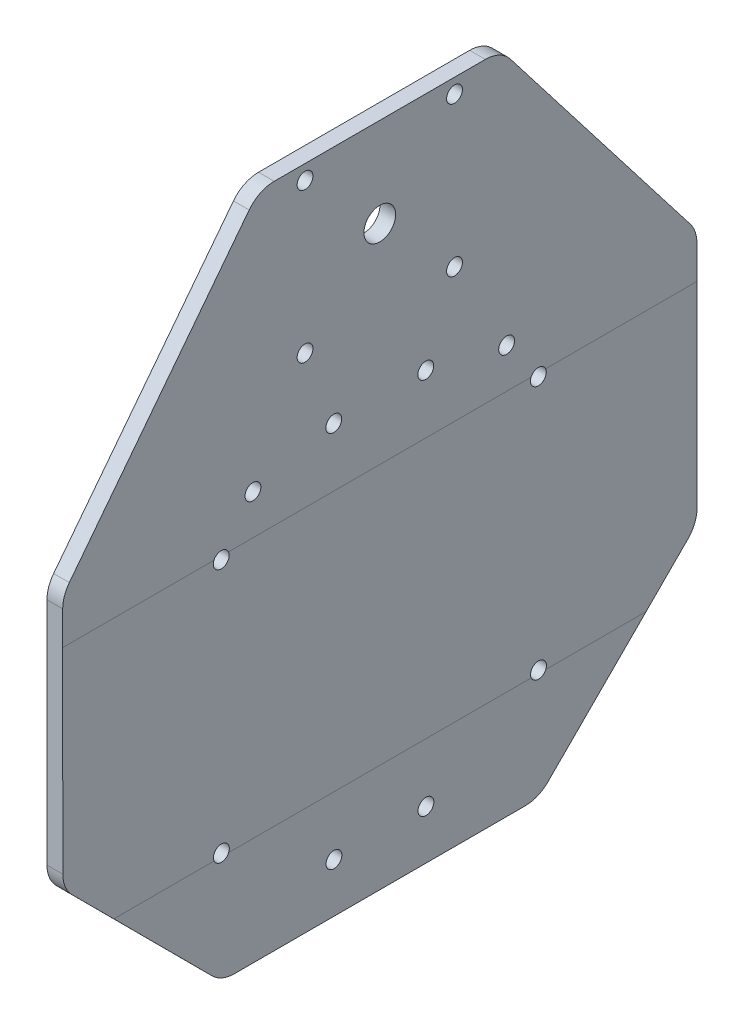
SolidWorks part; units mm, degrees
ref_plane "Alzado" through (0, 0, 0) normal (0, 0, 1) x (1, 0, 0)
ref_plane "Planta" through (0, 0, 0) normal (0, 1, 0) x (1, 0, 0)
ref_plane "Vista lateral" through (0, 0, 0) normal (1, 0, 0) x (0, 0, -1)
sketch "Croquis1" plane through (0, 0, 0) normal (0, 0, 1) x (1, 0, 0)
  line L0 (108.156, -24.4012) -> (108.156, 35.6988) construction
  line L5 (108.156, -24.4012) -> (-28.444, -24.4012) construction
  line L6 (108.156, 35.6988) -> (-28.444, 35.6988) construction
  line L7 (-28.444, -24.4012) -> (-28.444, 35.6988) construction
  line L8 (39.856, 35.6988) -> (39.856, -24.4012) construction
  line L9 (78.056, 5.6488) -> (108.156, 5.6488) construction
  line L10 (81.056, -24.4012) -> (89.106, -24.4012) construction
  line L11 (78.056, -21.4012) -> (78.056, -12.9012) construction
  line L12 (81.056, 35.6988) -> (89.106, 35.6988) construction
  line L13 (108.156, -21.4012) -> (108.156, -12.9012) construction
  line L14 (78.056, -24.4012) -> (108.156, 35.6988) construction
  line L15 (78.056, 35.6988) -> (108.156, -24.4012) construction
  line L16 (89.106, 35.6988) -> (89.106, 33.3988) construction
  line L17 (88.106, 13.6988) -> (98.106, 13.6988) construction
  line L18 (86.606, 15.1988) -> (86.606, 25.1988) construction
  line L19 (88.106, 26.6988) -> (98.106, 26.6988) construction
  line L20 (99.606, 15.1988) -> (99.606, 25.1988) construction
  line L21 (86.606, 13.6988) -> (99.606, 26.6988) construction
  line L22 (86.606, 26.6988) -> (99.606, 13.6988) construction
  line L23 (108.156, 24.1988) -> (108.156, 32.6988) construction
  line L24 (89.756, 16.8488) -> (96.456, 16.8488) construction
  line L25 (89.756, 16.8488) -> (89.756, 23.5488) construction
  line L26 (89.756, 23.5488) -> (96.456, 23.5488) construction
  line L27 (96.456, 16.8488) -> (96.456, 23.5488) construction
  line L28 (89.756, 16.8488) -> (96.456, 23.5488) construction
  line L29 (89.756, 23.5488) -> (96.456, 16.8488) construction
  line L30 (81.406, -22.1012) -> (89.106, -22.1012) construction
  line L31 (80.356, -20.1512) -> (80.356, -12.9012) construction
  line L32 (81.406, 33.3988) -> (89.106, 33.3988) construction
  line L33 (105.856, -20.1512) -> (105.856, -12.9012) construction
  line L34 (80.356, -22.1012) -> (105.856, 33.3988) construction
  line L35 (80.356, 33.3988) -> (105.856, -22.1012) construction
  line L36 (97.106, 35.6988) -> (97.106, 33.3988) construction
  line L37 (105.856, 24.1988) -> (105.856, 31.4488) construction
  line L38 (78.056, 24.1988) -> (80.356, 24.1988) construction
  line L39 (78.056, 16.1988) -> (80.356, 16.1988) construction
  line L40 (108.156, 16.1988) -> (105.856, 16.1988) construction
  line L41 (108.156, 24.1988) -> (105.856, 24.1988) construction
  line L42 (88.106, 26.6988) -> (81.406, 33.3988) construction
  line L43 (86.606, 26.6988) -> (80.356, 33.3988) construction
  line L44 (86.606, 25.1988) -> (80.356, 31.4488) construction
  line L45 (99.606, 25.1988) -> (105.856, 31.4488) construction
  line L46 (98.106, 26.6988) -> (104.806, 33.3988) construction
  line L47 (99.606, -13.9012) -> (105.856, -20.1512) construction
  line L48 (98.106, -15.4012) -> (104.806, -22.1012) construction
  line L49 (78.056, -24.4012) -> (89.106, -24.4012) construction
  line L50 (78.056, 35.6988) -> (89.106, 35.6988) construction
  line L51 (86.606, -13.9012) -> (80.356, -20.1512) construction
  line L52 (88.106, -15.4012) -> (81.406, -22.1012) construction
  line L53 (97.106, -24.4012) -> (97.106, -22.1012) construction
  line L54 (89.106, -24.4012) -> (89.106, -22.1012) construction
  line L55 (78.056, -4.9012) -> (80.356, -4.9012) construction
  line L56 (78.056, -12.9012) -> (80.356, -12.9012) construction
  line L57 (108.156, -12.9012) -> (105.856, -12.9012) construction
  line L58 (108.156, -4.9012) -> (105.856, -4.9012) construction
  line L59 (89.756, -5.5512) -> (89.756, -12.2512) construction
  line L60 (89.756, -12.2512) -> (96.456, -12.2512) construction
  line L61 (96.456, -5.5512) -> (96.456, -12.2512) construction
  line L62 (89.756, -5.5512) -> (96.456, -5.5512) construction
  line L63 (88.106, -2.4012) -> (98.106, -2.4012) construction
  line L64 (99.606, -3.9012) -> (99.606, -13.9012) construction
  line L65 (86.606, -3.9012) -> (86.606, -13.9012) construction
  line L66 (88.106, -15.4012) -> (98.106, -15.4012) construction
  line L67 (97.106, -24.4012) -> (105.156, -24.4012) construction
  line L68 (99.606, -3.9012) -> (105.856, 2.3488) construction
  line L69 (98.106, -2.4012) -> (104.806, 4.2988) construction
  line L70 (88.106, -2.4012) -> (81.406, 4.2988) construction
  line L71 (86.606, -3.9012) -> (80.356, 2.3488) construction
  line L72 (81.406, 4.2988) -> (80.356, 5.3488) construction
  line L73 (104.806, 4.2988) -> (105.856, 5.3488) construction
  line L74 (80.356, 5.3488) -> (80.356, 5.9488) construction
  line L75 (105.856, 5.3488) -> (105.856, 5.9488) construction
  line L76 (99.606, 15.1988) -> (105.856, 8.9488) construction
  line L77 (98.106, 13.6988) -> (104.806, 6.9988) construction
  line L78 (86.606, 15.1988) -> (80.356, 8.9488) construction
  line L79 (88.106, 13.6988) -> (81.406, 6.9988) construction
  line L80 (81.406, 6.9988) -> (80.356, 5.9488) construction
  line L81 (104.806, 6.9988) -> (105.856, 5.9488) construction
  line L82 (80.356, 8.9488) -> (80.356, 16.1988) construction
  line L83 (105.856, 8.9488) -> (105.856, 16.1988) construction
  line L84 (108.156, -4.9012) -> (108.156, 16.1988) construction
  line L85 (105.856, -4.9012) -> (105.856, 2.3488) construction
  line L86 (78.056, -4.9012) -> (78.056, 16.1988) construction
  line L87 (80.356, -4.9012) -> (80.356, 2.3488) construction
  line L88 (97.106, -24.4012) -> (108.156, -24.4012) construction
  line L89 (97.106, -22.1012) -> (104.806, -22.1012) construction
  line L90 (97.106, 35.6988) -> (105.156, 35.6988) construction
  line L91 (97.106, 35.6988) -> (108.156, 35.6988) construction
  line L92 (97.106, 33.3988) -> (104.806, 33.3988) construction
  line L93 (80.356, 24.1988) -> (80.356, 31.4488) construction
  line L94 (78.056, 24.1988) -> (78.056, 32.6988) construction
  line L95 (93.106, 46.6988) -> (90.106, 46.6988) construction
  line L96 (90.106, 46.6988) -> (90.106, 49.1488) construction
  line L97 (90.106, 58.6988) -> (96.106, 58.6988) construction
  line L98 (93.106, 58.6988) -> (93.106, 46.6988) construction
  line L99 (90.106, 58.6988) -> (88.006, 56.5988) construction
  line L100 (90.106, 46.6988) -> (90.106, 49.1488) construction
  line L101 (93.106, 46.6988) -> (90.106, 49.1488) construction
  line L102 (96.106, 49.1488) -> (98.206, 49.1488) construction
  line L103 (93.106, 46.6988) -> (88.006, 46.6988) construction
  line L104 (88.006, 36.7988) -> (88.006, 56.5988) construction
  line L105 (90.106, 49.1488) -> (96.106, 49.1488) construction
  line L106 (90.106, 49.1488) -> (88.006, 49.1488) construction
  line L107 (98.206, 36.7988) -> (98.206, 56.5988) construction
  line L108 (96.106, 58.6988) -> (98.206, 56.5988) construction
  line L109 (93.106, 46.6988) -> (98.206, 46.6988) construction
  line L110 (98.206, 46.6988) -> (108.206, 46.6988) construction
  line L111 (96.106, 34.6988) -> (98.206, 36.7988) construction
  line L112 (90.106, 34.6988) -> (96.106, 34.6988) construction
  line L113 (90.106, 34.6988) -> (88.006, 36.7988) construction
  line L114 (108.206, 46.6988) -> (113.206, 46.6988) construction
  line L115 (108.156, -35.4012) -> (113.156, -35.4012) construction
  line L116 (113.206, 46.6988) -> (113.156, -35.4012) construction
  line L117 (113.206, 46.6988) -> (118.156, 46.6988) construction
  line L118 (118.156, 46.6988) -> (118.156, -35.4012) construction
  line L119 (118.156, -35.4012) -> (113.156, -35.4012) construction
  line L121 (-38.444, 46.6988) -> (-38.444, -35.4012)
  line L122 (-33.494, 46.6988) -> (-33.444, -35.4012)
  line L124 (-38.444, 46.6988) -> (-38.444, 80.6988)
  line L125 (-38.444, 80.6988) -> (-33.494, 80.6988)
  line L126 (-33.494, 80.6988) -> (-33.494, 46.6988)
  line L127 (-33.444, -35.4012) -> (-33.444, -69.4012)
  line L128 (-33.444, -69.4012) -> (-38.444, -69.4012)
  line L129 (-38.444, -69.4012) -> (-38.444, -35.4012)
  line L130 (-33.4904, 40.6988) -> (39.856, 40.6988) construction
  line L131 (-33.494, 80.6988) -> (39.856, 80.6988) construction
  line L132 (39.856, 80.6988) -> (39.856, 40.6988) construction
  line L133 (39.856, 5.6488) -> (-28.444, 5.6488) construction
  line L134 (-33.444, -69.4012) -> (39.856, -69.4012) construction
  line L135 (39.856, -69.4012) -> (39.856, -29.4012) construction
  line L136 (39.856, -29.4012) -> (-33.4477, -29.4012) construction
  arc A4 (81.056, -24.4012) -> (78.056, -21.4012) centre (81.056, -21.4012) cw construction
  arc A5 (105.156, -24.4012) -> (108.156, -21.4012) centre (105.156, -21.4012) ccw construction
  arc A6 (105.156, 35.6988) -> (108.156, 32.6988) centre (105.156, 32.6988) cw construction
  arc A7 (78.056, 32.6988) -> (81.056, 35.6988) centre (81.056, 32.6988) cw construction
  circle A8 centre (93.106, 20.1988) radius 3.35 construction
  circle A9 centre (93.106, -8.9012) radius 3.35 construction
  point P0 (0, 0)
  point P15 (93.106, 49.1488)
  point P21 (93.106, 5.6488)
  point P28 (93.106, 20.1988)
  point P29 (93.106, 20.1988)
  point P40 (93.106, 5.6488)
  point P75 (93.106, 16.8488)
  point P92 (93.106, -5.5512)
  dimension "D5" = 10.2
  dimension "D19" = 3
  dimension "D2" = 136.6
  dimension "D3" = 9.9
  dimension "D4" = 45
  dimension "D6" = 60.1
  dimension "D7" = 30.1
  dimension "D8" = 13
  dimension "D9" = 13
  dimension "D10" = 22
  dimension "D11" = 6.7
  dimension "D12" = 6.7
  dimension "D13" = 25.5
  dimension "D14" = 55.5
  dimension "D15" = 1.5
  dimension "D16" = 135
  dimension "D17" = 1.5
  dimension "D18" = 135
  dimension "D20" = 12
  dimension "D21" = 10
  dimension "D22" = 7.7
  dimension "D23" = 1
  dimension "D24" = 5
  dimension "D25" = 5
  dimension "D26" = 11
  dimension "D27" = 5
  dimension "D28" = 40
  dimension "D29" = 5
  dimension "D30" = 5
  dimension "D31" = 40
extrude "Saliente-Extruir1" add sketch "Croquis1" along normal blind 200 contours L121 L129 L128 L127 L122 L126 L125 L124
sketch "Croquis2" plane through (-38.444, 0, 0) normal (-1, 0, 0) x (0, 0, 1)
  line L0 (200, 5.6488) -> (0, 5.6488) construction
  line L1 (200, -69.4012) -> (0, -69.4012) construction
  line L2 (200, -69.4012) -> (200, 80.6988) construction
  line L3 (200, 80.6988) -> (0, 80.6988) construction
  line L4 (0, -69.4012) -> (0, 80.6988) construction
  line L5 (100, 80.6988) -> (100, -69.4012) construction
  line L6 (70, 80.6988) -> (70, 49.6988) construction
  line L7 (70, 49.6988) -> (130, 49.6988) construction
  line L8 (130, 49.6988) -> (130, 80.6988) construction
  circle A0 centre (150, 45.6988) radius 12 construction
  circle A1 centre (50, 45.6988) radius 12 construction
  circle A2 centre (85.5, 65.1988) radius 2.5
  circle A3 centre (114.5, 65.1988) radius 2.5
  circle A4 centre (50, 45.6988) radius 2.5
  circle A5 centre (150, 45.6988) radius 2.5
  circle A6 centre (150, -34.4012) radius 2.5
  circle A7 centre (150, -34.4012) radius 12 construction
  circle A8 centre (114.5, -53.9012) radius 2.5
  circle A9 centre (85.5, -53.9012) radius 2.5
  circle A10 centre (50, -34.4012) radius 2.5
  circle A11 centre (50, -34.4012) radius 12 construction
  point P14 (100, 49.6988)
  point P24 (70, 65.1988)
  point P26 (130, 65.1988)
  dimension "D5" = 15.5
  dimension "D7" = 5
  dimension "D8" = 5
  dimension "D9" = 5
  dimension "D10" = 5
  dimension "D1" = 31
  dimension "D2" = 60
  dimension "D3" = 40.05
  dimension "D4" = 20
  dimension "D6" = 15.5
extrude "Cortar-Extruir1" cut sketch "Croquis2" against normal blind 100
sketch "Croquis3" plane through (0, 80.6988, 0) normal (0, 1, 0) x (1, 0, 0)
  line L1 (-33.494, 0) -> (-38.444, 0)
  line L2 (-33.494, 0) -> (-33.494, -200)
  line L3 (-33.494, -200) -> (-38.444, -200)
  line L4 (-38.444, 0) -> (-38.444, -200)
extrude "Saliente-Extruir2" add sketch "Croquis3" along normal blind 60
sketch "Croquis4" plane through (-38.444, 0, 0) normal (-1, 0, 0) x (0, 0, 1)
  line L0 (100, 140.6988) -> (100, 84.2988) construction
  line L1 (0, 140.6988) -> (200, 140.6988) construction
  line L2 (100, 84.2988) -> (100, -69.4012) construction
  line L3 (71.8, 84.2988) -> (128.2, 84.2988) construction
  line L4 (71.8, 84.2988) -> (71.8, 140.6988) construction
  line L5 (71.8, 140.6988) -> (128.2, 140.6988) construction
  line L6 (128.2, 84.2988) -> (128.2, 140.6988) construction
  line L7 (71.8, 84.2988) -> (128.2, 140.6988) construction
  line L8 (71.8, 140.6988) -> (128.2, 84.2988) construction
  line L9 (76.43, 136.0688) -> (123.57, 136.0688) construction
  line L10 (76.43, 136.0688) -> (76.43, 88.9288) construction
  line L11 (76.43, 88.9288) -> (123.57, 88.9288) construction
  line L12 (123.57, 136.0688) -> (123.57, 88.9288) construction
  line L13 (76.43, 136.0688) -> (123.57, 88.9288) construction
  line L14 (76.43, 88.9288) -> (123.57, 136.0688) construction
  line L15 (200, -69.4012) -> (0, -69.4012) construction
  line L16 (100, 59.2988) -> (200, 59.2988) construction
  line L17 (200, -69.4012) -> (200, 140.6988) construction
  line L18 (100, 59.2988) -> (0, 59.2988) construction
  line L19 (0, 140.6988) -> (0, -69.4012) construction
  line L20 (61.8, 140.6988) -> (0, 60.6988)
  line L21 (0, -19.3012) -> (50, -69.4012)
  line L22 (200, -19.3012) -> (150, -69.4012)
  line L23 (138.2, 140.6988) -> (200, 60.6988)
  line L24 (0, 60.6988) -> (0, 140.6988)
  line L25 (0, 140.6988) -> (61.8, 140.6988)
  line L26 (138.2, 140.6988) -> (200, 140.6988)
  line L27 (200, 140.6988) -> (200, 60.6988)
  line L28 (200, -19.3012) -> (200, -69.4012)
  line L29 (200, -69.4012) -> (150, -69.4012)
  line L30 (50, -69.4012) -> (0, -69.4012)
  line L31 (0, -69.4012) -> (0, -19.3012)
  circle A0 centre (76.43, 136.0688) radius 2.5
  circle A1 centre (123.57, 136.0688) radius 2.5
  circle A2 centre (76.43, 88.9288) radius 2.5
  circle A3 centre (123.57, 88.9288) radius 2.5
  circle A4 centre (100, 112.4988) radius 5
  circle A5 centre (60, 59.2988) radius 2.5
  circle A6 centre (140, 59.2988) radius 2.5
  point P4 (100, 112.4988)
  point P9 (100, 112.4988)
  dimension "D5" = 5
  dimension "D6" = 5
  dimension "D7" = 5
  dimension "D8" = 5
  dimension "D9" = 10
  dimension "D10" = 5
  dimension "D1" = 56.4
  dimension "D2" = 56.4
  dimension "D3" = 47.14
  dimension "D4" = 47.14
  dimension "D11" = 80
  dimension "D12" = 25
  dimension "D13" = 80
  dimension "D14" = 10
  dimension "D15" = 80
  dimension "D16" = 100
extrude "Cortar-Extruir2" cut sketch "Croquis4" against normal blind 60
fillet "Redondeo1" radius 10 8 edges at (-35.969, 140.6988, 138.2) (-35.969, 140.6988, 61.8) (-35.944, -69.4012, 150) (-35.944, -69.4012, 50) (-35.9489, -19.3012, 0) (-35.969, 60.6988, 0) (-35.9489, -19.3012, 200) (-35.969, 60.6988, 200)
